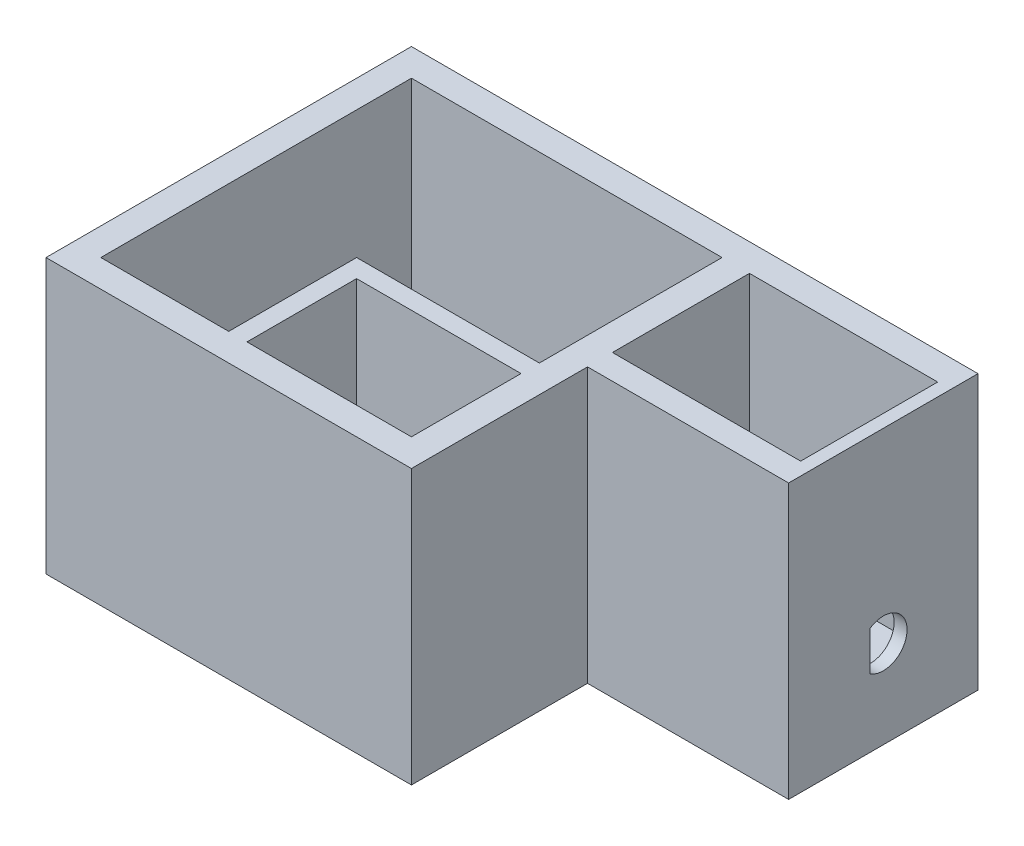
SolidWorks part; units mm, degrees
ref_plane "Alzado" through (0, 0, 0) normal (0, 0, 1) x (1, 0, 0)
ref_plane "Planta" through (0, 0, 0) normal (0, 1, 0) x (1, 0, 0)
ref_plane "Vista lateral" through (0, 0, 0) normal (1, 0, 0) x (0, 0, -1)
sketch "Croquis2" plane through (0, 0, 0) normal (0, 1, 0) x (1, 0, 0)
  line L1 (-50, 50) -> (50, 50)
  line L2 (-50, 50) -> (-50, -50)
  line L3 (-50, -50) -> (50, -50)
  line L4 (50, 50) -> (50, -50)
  line L5 (-50, 50) -> (50, -50) construction
  line L6 (-50, -50) -> (50, 50) construction
  point P0 (0, 0)
  dimension "D1" = 100
  dimension "D2" = 100
extrude "Saliente-Extruir1" add sketch "Croquis2" along normal blind 75
sketch "Croquis3" plane through (0, 75, 0) normal (0, 1, 0) x (1, 0, 0)
  line L1 (-42.5, 42.5) -> (42.5, 42.5)
  line L2 (-42.5, 42.5) -> (-42.5, -42.5)
  line L3 (-42.5, -42.5) -> (42.5, -42.5)
  line L4 (42.5, 42.5) -> (42.5, -42.5)
  line L5 (-42.5, 42.5) -> (42.5, -42.5) construction
  line L6 (-42.5, -42.5) -> (42.5, 42.5) construction
  point P0 (0, 0)
  dimension "D1" = 85
  dimension "D2" = 85
extrude "Cortar-Extruir1" cut sketch "Croquis3" against normal blind 65
sketch "Croquis4" plane through (0, 10, 0) normal (0, 1, 0) x (1, 0, 0)
  line L1 (42.5, -42.5) -> (-7.5, -42.5)
  line L2 (42.5, -42.5) -> (42.5, -7.5)
  line L3 (42.5, -7.5) -> (-7.5, -7.5)
  line L4 (-7.5, -42.5) -> (-7.5, -7.5)
  dimension "D1" = 35
  dimension "D2" = 50
extrude "Saliente-Extruir2" add sketch "Croquis4" along normal through all
sketch "Croquis5" plane through (0, 75, 0) normal (0, 1, 0) x (1, 0, 0)
  line L0 (-7.5, -42.5) -> (-2.5102, -42.5)
  line L2 (-2.5102, -42.5) -> (42.4898, -42.5)
  line L3 (-2.5102, -42.5) -> (-2.5102, -12.5)
  line L4 (-2.5102, -12.5) -> (42.4898, -12.5)
  line L5 (42.4898, -42.5) -> (42.4898, -12.5)
  dimension "D1" = 45
  dimension "D2" = 30
extrude "Cortar-Extruir2" cut sketch "Croquis5" against normal blind 65 and the other way through all contours L2 L5 L4 L3
sketch "Croquis6" plane through (-2.5102, 0, 0) normal (1, 0, 0) x (0, 0, -1)
  line L0 (-42.5, 10) -> (-12.5, 10) construction
  line L1 (-27.5, 10) -> (-42.5, 10)
  line L2 (-27.5, 10) -> (-27.5, 20.847)
  line L3 (-27.5, 20.847) -> (-42.5, 20.847)
  line L4 (-42.5, 10) -> (-42.5, 20.847)
  line L5 (-42.5, 75) -> (-42.5, 10) construction
extrude "Cortar-Extruir3" cut sketch "Croquis6" against normal blind 16
sketch "Croquis7" plane through (50, 0, 0) normal (1, 0, 0) x (0, 0, -1)
  line L0 (0, 0) -> (0, 10)
  line L1 (-50, 0) -> (50, 0) construction
  line L3 (0, 10) -> (28.6178, 10)
  line L4 (0, 10) -> (0, 17.7886)
  line L5 (0, 17.7886) -> (28.6178, 17.7886)
  line L6 (28.6178, 10) -> (28.6178, 17.7886)
extrude "Cortar-Extruir4" cut sketch "Croquis7" against normal blind 11 contours L3 L6 L5 L4
sketch "Croquis8" plane through (0, 0, 0) normal (0, -1, 0) x (1, 0, 0)
  line L0 (50, 50) -> (50, -50) construction
  line L1 (50, -50) -> (105.03, -50)
  line L2 (50, -50) -> (50, 1.8219)
  line L3 (50, 1.8219) -> (105.03, 1.8219)
  line L4 (105.03, -50) -> (105.03, 1.8219)
extrude "Saliente-Extruir3" add sketch "Croquis8" against normal through all
sketch "Croquis9" plane through (0, 75, 0) normal (0, 1, 0) x (1, 0, 0)
  line L1 (42.5, 42.5) -> (50, 42.5)
  line L3 (50, 42.5) -> (101.5, 42.5)
  line L4 (50, 42.5) -> (50, 5)
  line L5 (50, 5) -> (101.5, 5)
  line L6 (101.5, 42.5) -> (101.5, 5)
  dimension "D1" = 51.5
  dimension "D2" = 37.5
extrude "Cortar-Extruir5" cut sketch "Croquis9" against normal blind 65 contours L6 L3 L4 L5
sketch "Croquis10" plane through (105.03, 0, 0) normal (1, 0, 0) x (0, 0, -1)
  line L0 (24.0891, 0) -> (24.0891, 24.0298)
  line L1 (50, 0) -> (-1.8219, 0) construction
  circle A0 centre (24.0891, 24.0298) radius 6.5
extrude "Cortar-Extruir6" cut sketch "Croquis10" against normal blind 43 contours A0
sketch "Croquis11" plane through (105.03, 0, 0) normal (1, 0, 0) x (0, 0, -1)
  line L1 (14.7807, 31.2101) -> (20.3975, 31.2101)
  line L2 (14.7807, 31.2101) -> (14.7807, 16.8495)
  line L3 (14.7807, 16.8495) -> (20.3975, 16.8495)
  line L4 (20.3975, 31.2101) -> (20.3975, 16.8495)
  line L5 (14.7807, 31.2101) -> (20.3975, 16.8495) construction
  line L6 (14.7807, 16.8495) -> (20.3975, 31.2101) construction
  circle A0 centre (24.0891, 24.0298) radius 6.5 construction
  point P0 (17.5891, 24.0298)
extrude "Saliente-Extruir9" add sketch "Croquis11" against normal blind 3.5
sketch "Croquis12" plane through (0, 0, -42.5) normal (0, 0, 1) x (1, 0, 0)
  line L1 (-42.5, 10) -> (-27.5, 10)
  line L2 (-42.5, 10) -> (-42.5, 25)
  line L3 (-42.5, 25) -> (-27.5, 25)
  line L4 (-27.5, 10) -> (-27.5, 25)
  dimension "D1" = 15
  dimension "D2" = 15
extrude "Cortar-Extruir7" cut sketch "Croquis12" against normal blind 10
